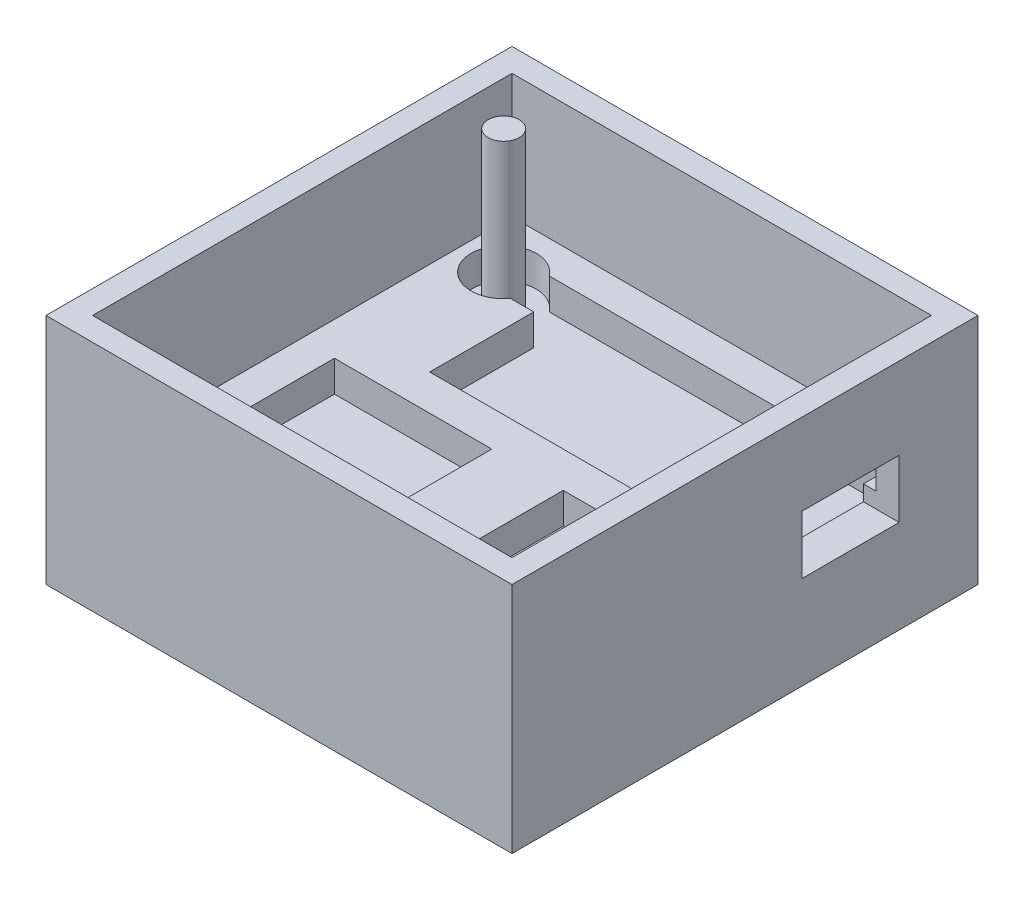
SolidWorks part; units mm, degrees
ref_plane "Front Plane" through (0, 0, 0) normal (0, 0, 1) x (1, 0, 0)
ref_plane "Top Plane" through (0, 0, 0) normal (0, 1, 0) x (1, 0, 0)
ref_plane "Right Plane" through (0, 0, 0) normal (1, 0, 0) x (0, 0, -1)
sketch "Sketch1" plane through (0, 0, 0) normal (0, 1, 0) x (1, 0, 0)
  line L1 (-38.1, -38.1) -> (38.1, -38.1)
  line L2 (-38.1, -38.1) -> (-38.1, 38.1)
  line L3 (-38.1, 38.1) -> (38.1, 38.1)
  line L4 (38.1, -38.1) -> (38.1, 38.1)
  line L5 (-38.1, -38.1) -> (38.1, 38.1) construction
  line L6 (-38.1, 38.1) -> (38.1, -38.1) construction
  point P0 (0, 0)
  dimension "D1" = 76.2
  dimension "D2" = 76.2
extrude "Boss-Extrude1" add sketch "Sketch1" along normal blind 38.1 contours L3 L4 L1 L2
ref_plane "Plane1" through (0, 38.1, 0) normal (0, 1, 0) x (1, 0, 0)
sketch "Sketch2" plane through (0, 38.1, 0) normal (0, 1, 0) x (1, 0, 0)
  line L0 (38.1, -38.1) -> (38.1, 38.1) construction
  line L1 (-19.05, 5.588) -> (32.258, 5.588)
  line L2 (-19.05, 5.588) -> (-19.05, 28.956)
  line L3 (-19.05, 28.956) -> (32.258, 28.956)
  line L4 (32.258, 5.588) -> (32.258, 28.956)
  line L5 (-19.05, 5.588) -> (32.258, 28.956) construction
  line L6 (-19.05, 28.956) -> (32.258, 5.588) construction
  line L7 (-38.1, 38.1) -> (38.1, 38.1) construction
  line L9 (8.636, -0.254) -> (32.258, -0.254)
  line L10 (8.636, -0.254) -> (8.636, -31.242)
  line L11 (8.636, -31.242) -> (32.258, -31.242)
  line L12 (32.258, -0.254) -> (32.258, -31.242)
  line L13 (8.636, -0.254) -> (32.258, -31.242) construction
  line L14 (8.636, -31.242) -> (32.258, -0.254) construction
  line L16 (-28.7782, -28.7782) -> (-3.048, -28.7782)
  line L17 (-28.7782, -28.7782) -> (-28.7782, -0.254)
  line L18 (-28.7782, -0.254) -> (-3.048, -0.254)
  line L19 (-3.048, -28.7782) -> (-3.048, -0.254)
  line L20 (-28.7782, -28.7782) -> (-3.048, -0.254) construction
  line L21 (-28.7782, -0.254) -> (-3.048, -28.7782) construction
  point P0 (6.604, 17.272)
  point P9 (20.447, -15.748)
  point P14 (0, 0)
  point P15 (0, 0)
  point P16 (-15.9131, -14.5161)
  point P21 (0, 0)
  dimension "D2" = 9.144
  dimension "D3" = 51.308
  dimension "D4" = 23.368
  dimension "D5" = 5.842
  dimension "D6" = 5.842
  dimension "D7" = 30.988
  dimension "D8" = 23.622
  dimension "D10" = 11.684
  dimension "D12" = 28.5242
  dimension "D13" = 25.7302
extrude "Cut-Extrude3" cut sketch "Sketch2" against normal blind 25.4
ref_plane "Plane2" through (0, 38.1, 0) normal (0, 1, 0) x (1, 0, 0)
sketch "Sketch8" plane through (0, 38.1, 0) normal (0, 1, 0) x (1, 0, 0)
  line L0 (-34.29, -34.29) -> (-34.29, 34.29)
  line L1 (-34.29, 34.29) -> (34.29, 34.29)
  line L2 (34.29, -34.29) -> (34.29, 34.29)
  line L3 (-34.29, -34.29) -> (34.29, -34.29)
  line L4 (-38.1, -38.1) -> (-38.1, 38.1) construction
  line L5 (-38.1, 38.1) -> (38.1, 38.1) construction
  line L6 (-38.1, -38.1) -> (38.1, -38.1) construction
  line L7 (38.1, -38.1) -> (38.1, 38.1) construction
  line L9 (-28.7782, -0.254) -> (-3.048, -0.254)
  line L10 (-28.7782, -0.254) -> (-28.7782, -28.7782)
  line L11 (-28.7782, -28.7782) -> (-3.048, -28.7782)
  line L12 (-3.048, -0.254) -> (-3.048, -28.7782)
  line L13 (8.636, -0.254) -> (32.258, -0.254)
  line L14 (8.636, -0.254) -> (8.636, -31.242)
  line L15 (8.636, -31.242) -> (32.258, -31.242)
  line L16 (32.258, -0.254) -> (32.258, -31.242)
  line L17 (-19.05, 28.956) -> (32.258, 28.956)
  line L18 (-19.05, 28.956) -> (-19.05, 5.588)
  line L19 (-19.05, 5.588) -> (32.258, 5.588)
  line L20 (32.258, 28.956) -> (32.258, 5.588)
  dimension "D1" = 3.81
  dimension "D2" = 3.81
  dimension "D3" = 3.81
  dimension "D4" = 3.81
extrude "Cut-Extrude5" cut sketch "Sketch8" against normal blind 20.32
ref_plane "Plane3" through (38.1, 0, 0) normal (1, 0, 0) x (0, 0, -1)
sketch "Sketch10" plane through (38.1, 0, 0) normal (1, 0, 0) x (0, 0, -1)
  line L1 (9.3345, 15.24) -> (25.2095, 15.24)
  line L2 (9.3345, 15.24) -> (9.3345, 24.765)
  line L3 (9.3345, 24.765) -> (25.2095, 24.765)
  line L4 (25.2095, 15.24) -> (25.2095, 24.765)
  line L5 (9.3345, 15.24) -> (25.2095, 24.765) construction
  line L6 (9.3345, 24.765) -> (25.2095, 15.24) construction
  line L7 (5.588, 12.7) -> (28.956, 12.7) construction
  point P0 (17.272, 20.0025)
  point P5 (0, 0)
  point P6 (0, 0)
  point P9 (17.272, 12.7)
  dimension "D1" = 15.875
  dimension "D2" = 9.525
  dimension "D3" = 2.54
extrude "Cut-Extrude6" cut sketch "Sketch10" against normal blind 20.32 contours L3 L4 L1 L2
ref_plane "Plane4" through (0, 17.78, 0) normal (0, 1, 0) x (1, 0, 0)
sketch "Sketch11" plane through (0, 17.78, 0) normal (0, 1, 0) x (1, 0, 0)
  line L0 (-19.05, 28.956) -> (-19.05, 22.606)
  line L1 (-19.05, 28.956) -> (-22.86, 28.956)
  line L2 (-19.05, 28.956) -> (-19.05, 5.588) construction
  line L3 (-19.05, 22.606) -> (-22.86, 22.606)
  line L4 (32.258, 28.956) -> (-19.05, 28.956) construction
  arc A0 (-22.86, 28.956) -> (-22.86, 22.606) centre (-27.1407, 25.781) ccw
  point P9 (-20.955, 22.606)
  dimension "D2" = 5.3297
  dimension "D1" = 6.35
  dimension "D3" = 3.81
extrude "Cut-Extrude7" cut sketch "Sketch11" against normal blind 5.08
ref_plane "Plane5" through (0, 12.7, 0) normal (0, 1, 0) x (1, 0, 0)
sketch "Sketch12" plane through (0, 12.7, 0) normal (0, 1, 0) x (1, 0, 0)
  circle A0 centre (-27.1407, 25.781) radius 2.54
  arc A1 (-22.86, 28.956) -> (-22.86, 22.606) centre (-27.1407, 25.781) ccw construction
  dimension "D1" = 5.08
extrude "Boss-Extrude2" add sketch "Sketch12" along normal up to surface (25.4 mm away) contours A0 up to face at (0, 38.1, 0)
